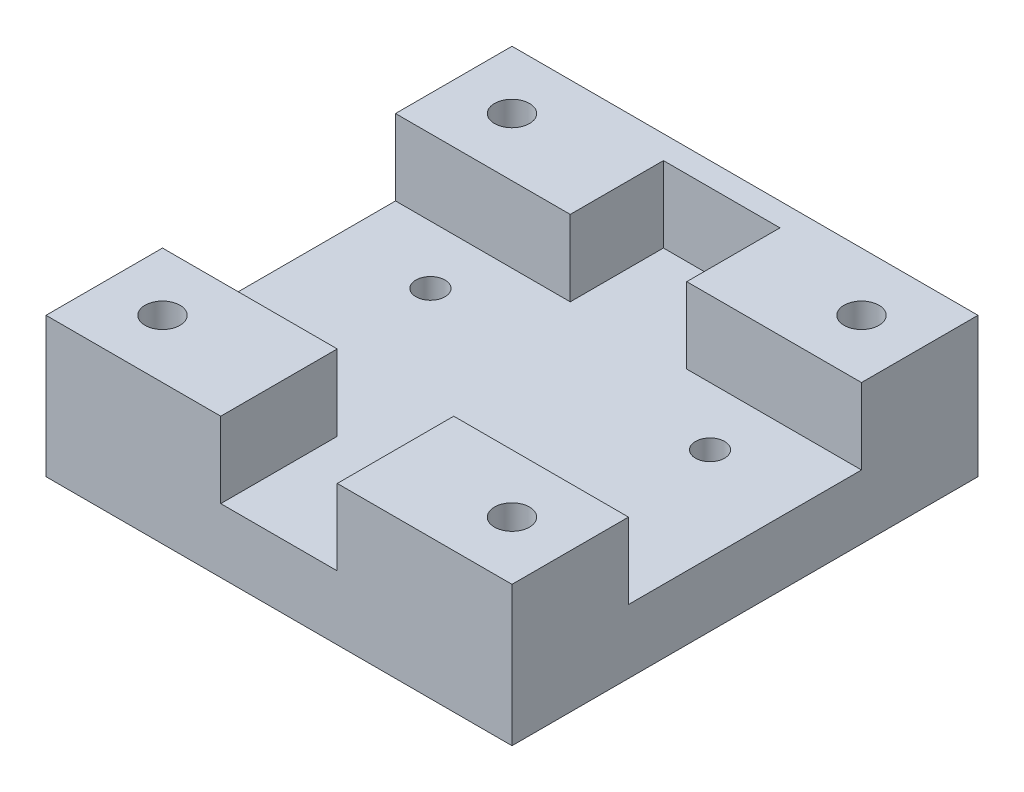
SolidWorks part; units mm, degrees
ref_plane "Plan de face" through (0, 0, 0) normal (0, 0, 1) x (1, 0, 0)
ref_plane "Plan de dessus" through (0, 0, 0) normal (0, 1, 0) x (1, 0, 0)
ref_plane "Plan de droite" through (0, 0, 0) normal (1, 0, 0) x (0, 0, -1)
sketch "Esquisse1" plane through (0, 0, 0) normal (0, 0, 1) x (1, 0, 0)
  line L0 (5, 0) -> (20, 0)
  line L1 (20, 0) -> (20, -12)
  line L2 (20, -12) -> (-20, -12)
  line L3 (-20, -12) -> (-20, 0)
  line L4 (-20, 0) -> (-5, 0)
  line L5 (5, 0) -> (5, -6.5)
  line L6 (5, -6.5) -> (-5, -6.5)
  line L7 (-5, -6.5) -> (-5, 0)
  dimension "D1" = 6.5
  dimension "D2" = 5
  dimension "D3" = 12
  dimension "D4" = 5
  dimension "D5" = 20
  dimension "D6" = 12
  dimension "D7" = 20
extrude "Boss.-Extru.1" add sketch "Esquisse1" along normal blind 40
sketch "Esquisse2" plane through (0, 0, 0) normal (0, 1, 0) x (1, 0, 0)
  line L0 (0, 0) -> (0, -40.0085) construction
  line L1 (-20, -20) -> (20, -20) construction
  line L2 (-20, -40) -> (-20, 0) construction
  line L3 (20, -40) -> (20, 0) construction
  line L4 (-5, -40) -> (-5, 0) construction
  circle A0 centre (-15, -5) radius 1.5
  circle A1 centre (-15, -35) radius 1.5
  circle A2 centre (15, -35) radius 1.5
  circle A3 centre (15, -5) radius 1.5
  circle A4 centre (-12, -25) radius 1.25
  circle A5 centre (-12, -15) radius 1.25
  circle A6 centre (12, -25) radius 1.25
  circle A7 centre (12, -15) radius 1.25
  dimension "D1" = 15
  dimension "D3" = 3
  dimension "D4" = 2.5
  dimension "D5" = 5
  dimension "D6" = 7
  dimension "D2" = 15
extrude "Enlèv. mat.-Extru.1" cut sketch "Esquisse2" against normal up to next
sketch "Esquisse3" plane through (0, 0, 0) normal (0, 1, 0) x (1, 0, 0)
  line L0 (0, 0) -> (0, -40) construction
  line L1 (5, -40) -> (-5, -40) construction
  line L2 (-20, -30) -> (-20, -10)
  line L3 (-20, -40) -> (-20, 0) construction
  line L4 (-20, -20) -> (20, -20) construction
  line L5 (20, -40) -> (20, 0) construction
  line L6 (-20, -10) -> (-5, -10)
  line L7 (-5, -40) -> (-5, 0) construction
  line L8 (-5, -10) -> (-5, -30)
  line L9 (-20, -30) -> (-5, -30)
  line L10 (20, -30) -> (5, -30)
  line L11 (5, -10) -> (5, -30)
  line L12 (20, -10) -> (5, -10)
  line L13 (20, -30) -> (20, -10)
  point P17 (-5, -20)
  dimension "D1" = 10
extrude "Enlèv. mat.-Extru.2" cut sketch "Esquisse3" against normal blind 6.5
sketch "Esquisse4" plane through (0, 0, 0) normal (0, 0, -1) x (-1, 0, 0)
  line L0 (-20, 0) -> (20, 0)
  line L1 (20, 0) -> (20, -12)
  line L2 (20, -12) -> (-20, -12)
  line L3 (-20, -12) -> (-20, 0)
extrude "Boss.-Extru.2" add sketch "Esquisse4" against normal blind 2
chamfer "Chanfrein1" distance 2 angle 45 4 edges at (10.75, -12, 15) (-13.25, -12, 15) (10.75, -12, 25) (-13.25, -12, 25)
